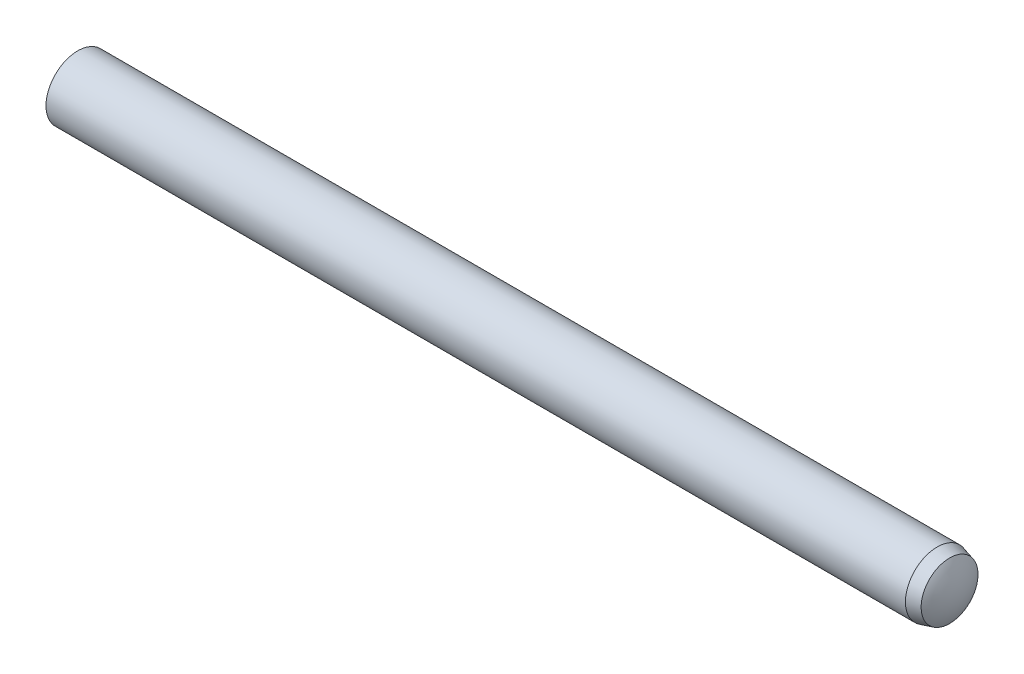
SolidWorks part; units mm, degrees
ref_plane "Front Plane" through (0, 0, 0) normal (0, 0, 1) x (1, 0, 0)
ref_plane "Top Plane" through (0, 0, 0) normal (0, 1, 0) x (1, 0, 0)
ref_plane "Right Plane" through (0, 0, 0) normal (1, 0, 0) x (0, 0, -1)
sketch "Sketch1" plane through (0, 0, 0) normal (0, 0, 1) x (1, 0, 0)
  line L0 (-35, 0) -> (35, 0) construction
  line L1 (35, 2.5) -> (35, -2.5) construction
  line L2 (-35, 2.5) -> (-35, -2.5) construction
  line L3 (33.375, 2.5) -> (33.375, -2.5) construction
  line L4 (-34.25, 2.5) -> (-34.25, -2.5) construction
  line L5 (-35, 0) -> (-34.25, 0) construction
  line L6 (35, 0) -> (33.375, 0) construction
  line L7 (34.35, 2.5) -> (34.35, -2.5) construction
  dimension "Dia" = 5
  dimension "Length" = 70
  dimension "D1" = 1.625
  dimension "D2" = 0.75
  dimension "D3" = 0.975
sketch "Sketch2" plane through (0, 0, 0) normal (1, 0, 0) x (0, 0, -1)
  circle A0 centre (0, 0) radius 2.5
extrude "Extrude1" add sketch "Sketch2" against normal up to vertex (35 mm away) and the other way up to vertex (35 mm away) up to point (-35, 0, 0) other way up to point (35, 0, 0)
sketch "Sketch5" plane through (0, 0, 0) normal (0, 0, 1) x (1, 0, 0)
  line L0 (33.375, 2.5) -> (33.375, 3)
  line L1 (33.375, 3) -> (35.5, 3)
  line L2 (35.5, 3) -> (35.5, 0)
  line L3 (35, 0) -> (35.5, 0)
  line L5 (-34.25, 2.5) -> (-34.25, 3)
  line L6 (-34.25, 3) -> (-35.5, 3)
  line L7 (-35.5, 3) -> (-35.5, 0)
  line L8 (33.375, 2.5) -> (34.35, 2.2387)
  line L10 (-35, 0) -> (-35.5, 0)
  line L11 (-35, 2.5) -> (-35, -2.5) construction
  line L13 (33.375, 2.5) -> (33.375, -2.5) construction
  line L15 (-35, 0) -> (35, 0) construction
  line L16 (34.35, 2.5) -> (34.35, -2.5) construction
  line L17 (35, 2.5) -> (35, -2.5) construction
  arc A0 (34.35, 2.2387) -> (35, 0) centre (30.8196, 0) cw
  arc A1 (-34.25, 2.5) -> (-35, 0) centre (-30.4583, 0) ccw
  dimension "D1" = 15
  dimension "D2" = 0.5
revolve "Cut-Revolve1" cut sketch "Sketch5" angle 360 about L0
equation "\"D1@Sketch1\" = \"Dia@Sketch1\"*.325"
equation "\"D2@Sketch1\" = \"Dia@Sketch1\"*.15"
equation "\"D3@Sketch1\" = \"D1@Sketch1\"*.6"
